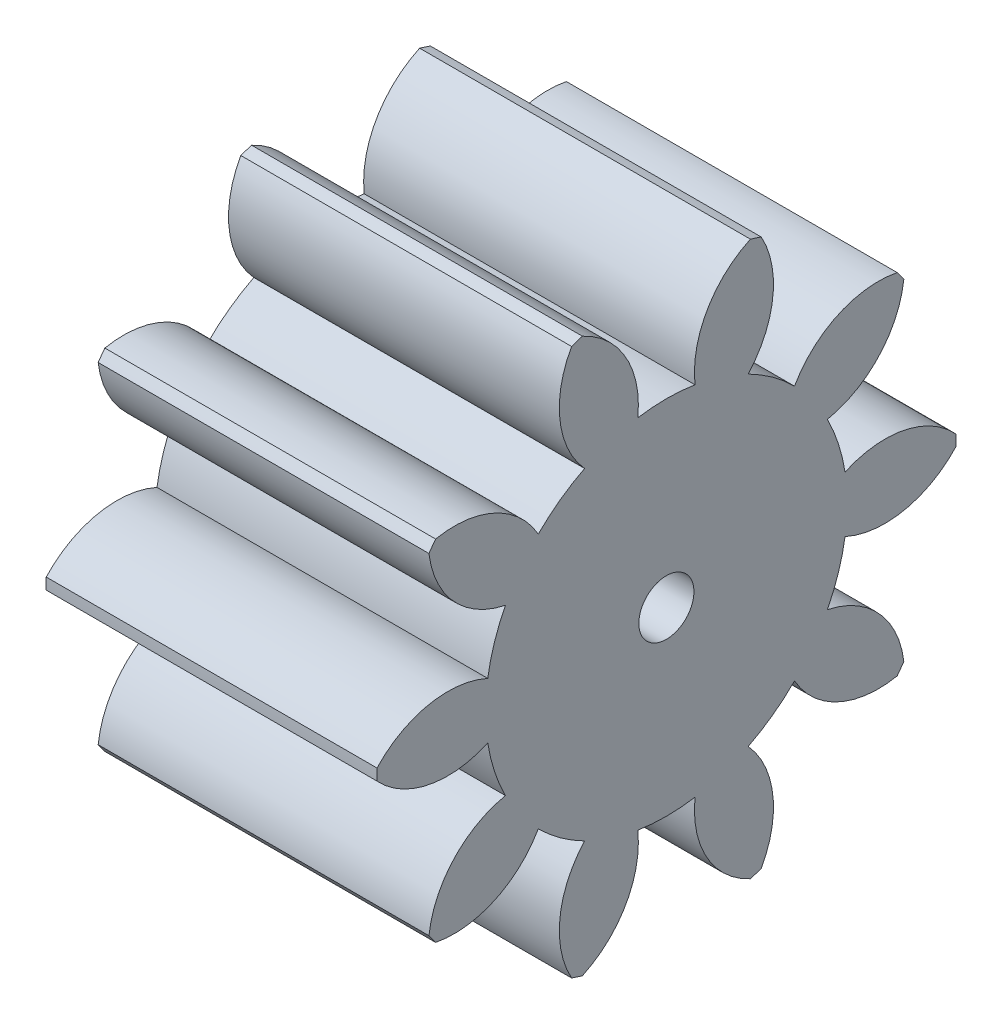
SolidWorks part; units mm, degrees
ref_plane "Plane1" through (0, 0, 0) normal (0, 0, 1) x (1, 0, 0)
ref_plane "Plane2" through (0, 0, 0) normal (0, 1, 0) x (1, 0, 0)
ref_plane "Plane3" through (0, 0, 0) normal (1, 0, 0) x (0, 0, -1)
sketch "HoldingSke" plane through (0, 0, 0) normal (0, 1, 0) x (1, 0, 0)
  line L0 (0, 0) -> (1.4069, -0.2481)
  line L1 (-15, 0) -> (100, 0) construction
  line L2 (0, 0) -> (-2.1039, 2.3779)
  line L3 (0, 0) -> (-11.863, 4.5341)
  line L4 (0, 0) -> (8.5048, 1.4996)
  line L5 (0, 0) -> (-46.8476, -17.4728)
  line L6 (0, 0) -> (-3.979, -2.6847)
  line L7 (-2.1039, 2.3779) -> (8.6586, 51.2059)
  line L8 (-76.2, 54.61) -> (-76.1, 54.61)
  line L9 (-71.009, 38.7566) -> (-53.1078, 45.2721)
  line L10 (-76.2, 71.12) -> (104.1128, 71.12)
  line L11 (0, 0) -> (-4.8, 0)
  line L12 (-76.2, 101.6) -> (-76.173, 101.6)
  line L13 (24.9733, 27.94) -> (52.9518, 28.4284)
  line L14 (24.9733, 27.94) -> (24.9743, 27.94)
  line L15 (24.9733, 27.94) -> (100.4006, 29.5858)
  line L16 (-63.627, -0.7) -> (-12.827, -0.7)
  circle A0 centre (0, 0) radius 0.4
  circle A1 centre (0, 0) radius 2.624
  circle A2 centre (0, 0) radius 37.5
  circle A3 centre (0, 0) radius 0.4
  dimension "MHD" = 5.248
  dimension "Hub_dia" = 75
  dimension "Bore" = 0.8
  dimension "MBD" = 0.8
  dimension "Num_teeth" = 10
  dimension "Pitch" = 1.4286
  dimension "Overall_len" = 50
  dimension "Show_teeth" = 10
  dimension "Thickness" = 4.8
  dimension "OAL" = 50.0001
  dimension "T_dim" = 0.1
  dimension "Ap" = 20
  dimension "H" = 19.05
  dimension "Pitch_radius" = 180.3128
  dimension "Width" = 4.8
  dimension "Backlash" = 0.027
  dimension "Addendum_fac" = 1
  dimension "Dedendum_fac" = 1.25
  dimension "Clearance_fac" = 0.25
  dimension "Dedendum_add" = 0.001
  dimension "Module" = 0.7
sketch "BasProSke" plane through (0, 0, 0) normal (0, 1, 0) x (1, 0, 0)
  line L0 (-10, 0) -> (60, 0) construction
  line L1 (0, 0) -> (0, 4.2)
  line L2 (0, 0) -> (4.8, 0)
  line L3 (4.8, 0) -> (4.8, 4.2)
  line L4 (4.8, 4.2) -> (0, 4.2)
  dimension "Thickness" = 4.8
  dimension "Diameter" = 8.4
revolve "Base-Revolve" add sketch "BasProSke" angle 360 about L0
sketch "TooCutSke" plane through (0, 0, 0) normal (1, 0, 0) x (0, 0, -1)
  line L1 (0, 0) -> (0, 107) construction
  line L2 (0, 0) -> (-0.5947, 3.4491) construction
  line L3 (0, 0) -> (-2.1409, 6.589) construction
  line L4 (-0.5947, 3.4491) -> (-1.0705, 3.2945) construction
  arc A0 (0.4155, 2.5909) -> (-0.4155, 2.5909) centre (0, 0) ccw
  arc A1 (1.2546, 4.0349) -> (-1.2546, 4.0349) centre (0, 0) ccw
  circle A2 centre (0, 0) radius 3.5 construction
  circle A3 centre (0, 0) radius 3.2889 construction
  arc A4 (-0.4155, 2.5909) -> (-1.2546, 4.0349) centre (-1.8066, 2.7483) ccw
  arc A5 (1.2546, 4.0349) -> (0.4155, 2.5909) centre (1.8066, 2.7483) ccw
  dimension "Root_dia" = 5.248
  dimension "Overcut_dia" = 8.4508
  dimension "Pitch_dia" = 7
  dimension "Base_dia" = 6.5778
  dimension "Flank_rad" = 1.4
  dimension "Half_ang" = 18
  dimension "Half_CT" = 0.5003
extrude "ToothCut" cut sketch "TooCutSke" along normal through all
fillet "Breaks" [suppressed] radius 0.014
fillet "RootFillets" [suppressed] radius 0.176
pattern_circular "TeethCuts" count 10 every 36 about axis through (-10, 0, 0) along (1, 0, 0) of "ToothCut", "RootFillets", "Breaks"
sketch "HubNeaOneSke" plane through (0, 0, 0) normal (-1, 0, 0) x (0, 0, 1)
  circle A0 centre (0, 0) radius 2.624
  dimension "Diameter" = 5.248
extrude "HubNearOne" [suppressed] add sketch "HubNeaOneSke" along normal blind 45.2001
sketch "HubNeaBotSke" plane through (0, 0, 0) normal (-1, 0, 0) x (0, 0, 1)
  circle A0 centre (0, 0) radius 2.624
  dimension "Diameter" = 5.248
extrude "HubNearBoth" [suppressed] add sketch "HubNeaBotSke" along normal blind 22.6
ref_plane "FarPln" through (4.8, 0, 0) normal (1, 0, 0) x (0, 0, -1)
sketch "HubFarSke" plane through (4.8, 0, 0) normal (1, 0, 0) x (0, 0, -1)
  circle A0 centre (0, 0) radius 2.624
  dimension "Diameter" = 5.248
extrude "HubFar" [suppressed] add sketch "HubFarSke" along normal blind 22.6
sketch "BorSke" plane through (0, 0, 0) normal (1, 0, 0) x (0, 0, -1)
  circle A0 centre (0, 0) radius 0.4
  dimension "Diameter" = 0.8
extrude "Bore" cut sketch "BorSke" along normal mid plane 100.0001
sketch "KeySke" plane through (0, 0, 0) normal (1, 0, 0) x (0, 0, -1)
  line L0 (-0.05, 0) -> (-0.05, 0.5)
  line L1 (-0.05, 0.5) -> (0.05, 0.5)
  line L2 (0.05, 0.5) -> (0.05, 0)
  line L3 (0, 0) -> (0, 34) construction
  line L4 (-0.05, 0) -> (0.05, 0)
  dimension "Offset" = 0.5
  dimension "Width" = 0.1
extrude "Keyway" [suppressed] cut sketch "KeySke" along normal mid plane 100.0001
pattern_circular "Keyway2" [suppressed] count 2 every 90 about axis through (-10, 0, 0) along (1, 0, 0)
equation "' \"Module@HoldingSke\" = 6.35"
equation "' \"Num_teeth@HoldingSke\" = 12"
equation "' \"Ap@HoldingSke\" =  20"
equation "' \"Ap@HoldingSke\" = 20"
equation "' \"Width@HoldingSke\" = 0.5 * 25.4"
equation "' \"Hub_dia@HoldingSke\"= 1 * 25.4"
equation "' \"Hub_dia@HoldingSke\" = 1 * 25.4"
equation "' \"Overall_len@HoldingSke\" = 1.0 * 25.4"
equation "' \"Bore@HoldingSke\" = 0.75 * 25.4"
equation "' \"T_dim@HoldingSke\" = 0.1 * 25.4"
equation "' \"Width@KeySke\" = 0.25 * 25.4"
equation "' \"Show_teeth@HoldingSke\" = 13"
equation "' \"Backlash@HoldingSke\" = 0.009 * 25.4"
equation "' \"Addendum_fac@HoldingSke\" = 1.0"
equation "' \"Dedendum_fac@HoldingSke\" = 1.25"
equation "' \"Dedendum_add@HoldingSke\" = 0.00005 * 25.4"
equation "' \"Clearance_fac@HoldingSke\" = 0.25"
equation "\"Pitch@HoldingSke\" = 1 / \"Module@HoldingSke\""
equation "\"Overcut_dia@TooCutSke\" = (\"Num_teeth@HoldingSke\" + 2 * \"Addendum_fac@HoldingSke\") / \"Pitch@HoldingSke\" + 0.002 * 25.4"
equation "\"Pitch_dia@TooCutSke\" = \"Num_teeth@HoldingSke\" / \"Pitch@HoldingSke\""
equation "\"Base_dia@TooCutSke\" = \"Num_teeth@HoldingSke\" / \"Pitch@HoldingSke\" * cos((\"Ap@HoldingSke\"  * 3.14159265 / 180))"
equation "\"Root_dia@TooCutSke\" = (\"Num_teeth@HoldingSke\" + 2) / \"Pitch@HoldingSke\" - 2 * (\"Addendum_fac@HoldingSke\" + \"Dedendum_fac@HoldingSke\") / \"Pitch@HoldingSke\" - \"Dedendum_add@HoldingSke\" * 2"
equation "\"Half_ang@TooCutSke\" = 180 / \"Num_teeth@HoldingSke\""
equation "\"Half_CT@TooCutSke\" = \"Num_teeth@HoldingSke\" / \"Pitch@HoldingSke\" * sin((3.14159265 / 2 / \"Num_teeth@HoldingSke\")) / 2 - 7 * \"Backlash@HoldingSke\" / 4"
equation "\"Flank_rad@TooCutSke\" = \"Num_teeth@HoldingSke\" / \"Pitch@HoldingSke\" / 5"
equation "\"Radius@RootFillets\" = \"Clearance_fac@HoldingSke\" / \"Pitch@HoldingSke\" + \"Dedendum_add@HoldingSke\""
equation "\"Break_rad@Breaks\" = 0.02 / \"Pitch@HoldingSke\""
equation "\"Thickness@HoldingSke\" = \"Width@HoldingSke\""
equation "\"OAL@HoldingSke\" = \"Thickness@HoldingSke\""
equation "\"MHD@HoldingSke\" = (\"Num_teeth@HoldingSke\" + 2) / \"Pitch@HoldingSke\" - 2 * (\"Addendum_fac@HoldingSke\" + \"Dedendum_fac@HoldingSke\")  / \"Pitch@HoldingSke\" - \"Dedendum_add@HoldingSke\" * 2"
equation "\"MBD@HoldingSke\" = (\"Num_teeth@HoldingSke\" + 2) / \"Pitch@HoldingSke\" - 2 * (\"Addendum_fac@HoldingSke\" + \"Dedendum_fac@HoldingSke\")  / \"Pitch@HoldingSke\" - \"Dedendum_add@HoldingSke\" * 2 - 0.002 * 25.4"
equation "\"MHD@HoldingSke\" = ((sgn( \"MHD@HoldingSke\" - \"Hub_dia@HoldingSke\" )-1)*( \"MHD@HoldingSke\" - \"Hub_dia@HoldingSke\" ))/-2+ \"Hub_dia@HoldingSke\""
equation "\"MBD@HoldingSke\" = ((sgn( \"MBD@HoldingSke\" - \"Bore@HoldingSke\" )-1)*( \"MBD@HoldingSke\" - \"Bore@HoldingSke\" ))/-2+ \"Bore@HoldingSke\""
equation "\"OAL@HoldingSke\" = ((sgn( \"OAL@HoldingSke\" - \"Overall_len@HoldingSke\" )+1)*( \"OAL@HoldingSke\" - \"Overall_len@HoldingSke\" ))/2 + \"Overall_len@HoldingSke\" + 0.000002 * 25.4"
equation "\"Num_teeth@TeethCuts\" = int( \"Show_teeth@HoldingSke\" ) + 1"
equation "\"Num_teeth@TeethCuts\" = ((sgn( \"Num_teeth@TeethCuts\" - \"Num_teeth@HoldingSke\" )-1)*( \"Num_teeth@TeethCuts\" - \"Num_teeth@HoldingSke\" ))/-2+ \"Num_teeth@HoldingSke\""
equation "\"Num_teeth@TeethCuts\" = ((sgn( \"Num_teeth@TeethCuts\" - 2.0)+1)*( \"Num_teeth@TeethCuts\" - 2.0))/2 +2.0"
equation "\"Angle@TeethCuts\" = 360.0 / \"Num_teeth@HoldingSke\""
equation "\"Diameter@BasProSke\" = (\"Num_teeth@HoldingSke\" + 2 * \"Addendum_fac@HoldingSke\") / \"Pitch@HoldingSke\""
equation "\"Thickness@BasProSke\"  = \"Thickness@HoldingSke\""
equation "' \"Fillet_rad@BasProSke\" =  \"Thickness@HoldingSke\" * 0.05"
equation "' \"Fillet_rad@BasProSke\" = \"Thickness@HoldingSke\" * 0.05"
equation "\"MHD@HoldingSke\" = ((sgn( \"MHD@HoldingSke\" - \"Root_dia@TooCutSke\" )-1)*( \"MHD@HoldingSke\" - \"Root_dia@TooCutSke\" ))/-2+ \"Root_dia@TooCutSke\""
equation "\"Diameter@HubNeaOneSke\" = \"MHD@HoldingSke\""
equation "\"Length@HubNearOne\" = \"OAL@HoldingSke\" - \"Thickness@BasProSke\""
equation "\"Diameter@HubNeaBotSke\" = \"MHD@HoldingSke\""
equation "\"Length@HubNearBoth\" = ( \"OAL@HoldingSke\" - \"Thickness@BasProSke\" ) / 2.0"
equation "\"Thickness@FarPln\" = \"Thickness@BasProSke\""
equation "\"Diameter@HubFarSke\" = \"MHD@HoldingSke\""
equation "\"Length@HubFar\" = ( \"OAL@HoldingSke\" - \"Thickness@BasProSke\" ) / 2.0"
equation "\"Diameter@BorSke\" = \"MBD@HoldingSke\""
equation "\"D1@Bore\" = \"OAL@HoldingSke\" * 2.0"
equation "\"D1@Keyway\" = \"OAL@HoldingSke\" * 2.0"
equation "\"Offset@KeySke\" = \"T_dim@HoldingSke\" + \"MBD@HoldingSke\" / 2.0"
